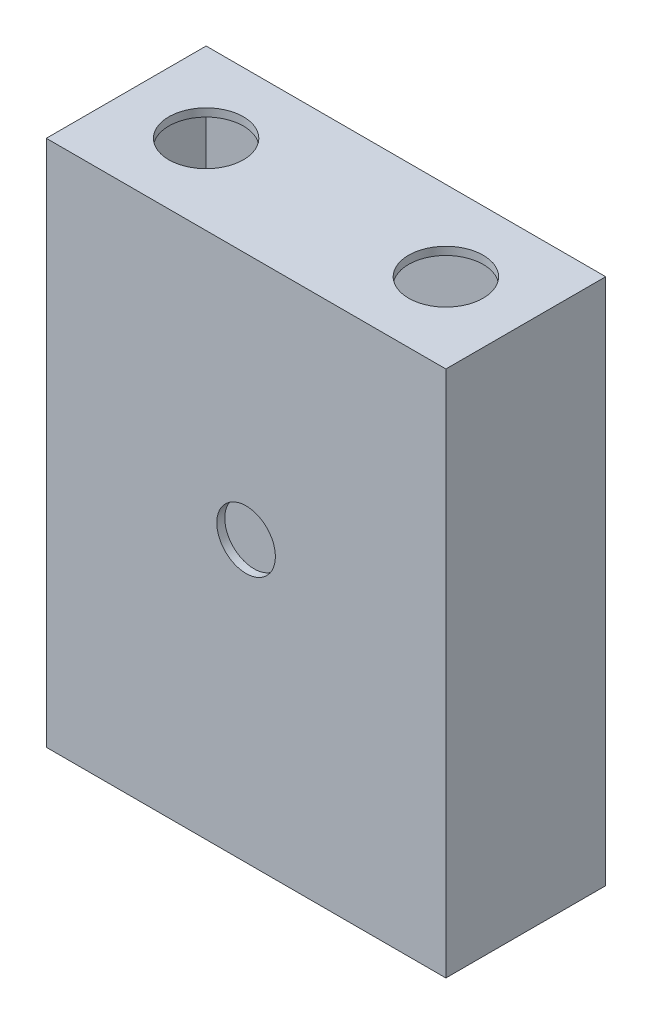
SolidWorks part; units mm, degrees
ref_plane "Alzado" through (0, 0, 0) normal (0, 0, 1) x (1, 0, 0)
ref_plane "Planta" through (0, 0, 0) normal (0, 1, 0) x (1, 0, 0)
ref_plane "Vista lateral" through (0, 0, 0) normal (1, 0, 0) x (0, 0, -1)
sketch "Croquis1" plane through (0, 0, 0) normal (0, 1, 0) x (1, 0, 0)
  line L1 (-120, -30) -> (120, -30)
  line L2 (-120, -30) -> (-120, 30)
  line L3 (-120, 30) -> (120, 30)
  line L4 (120, -30) -> (120, 30)
  line L5 (-120, -30) -> (120, 30) construction
  line L6 (-120, 30) -> (120, -30) construction
  circle A0 centre (0, 0) radius 14
  circle A1 centre (-90, 0) radius 14
  point P0 (0, 0)
  dimension "D3" = 28
  dimension "D4" = 28
  dimension "D5" = 30
  dimension "D6" = 90
  dimension "D1" = 240
  dimension "D2" = 60
extrude "Saliente-Extruir1" add sketch "Croquis1" along normal blind 3
sketch "Croquis4" plane through (0, 3, 0) normal (0, 1, 0) x (1, 0, 0)
  line L0 (-120, -30) -> (120, -30) construction
  line L1 (120, 30) -> (30, 30)
  line L2 (120, 30) -> (120, -30)
  line L3 (120, -30) -> (30, -30)
  line L4 (30, 30) -> (30, -30)
  dimension "D1" = 90
  dimension "D2" = 30
extrude "Cortar-Extruir2" cut sketch "Croquis4" against normal blind 5
sketch "Croquis2" plane through (0, 0, 0) normal (0, -1, 0) x (1, 0, 0)
  line L8 (-117, -27) -> (-117, 27)
  line L9 (-120, -30) -> (30, -30)
  line L10 (-120, -30) -> (-120, 30)
  line L11 (-120, 30) -> (30, 30)
  line L12 (30, -30) -> (30, 30)
  line L13 (-117, 27) -> (27, 27)
  line L14 (27, -27) -> (27, 27)
  line L15 (-117, -27) -> (27, -27)
  dimension "D1" = 3
extrude "Saliente-Extruir2" add sketch "Croquis2" along normal blind 195
sketch "Croquis5" plane through (0, 0, 30) normal (0, 0, 1) x (1, 0, 0)
  line L0 (-45, -195) -> (-45, -90) construction
  line L1 (30, -195) -> (-120, -195) construction
  circle A0 centre (-45, -90) radius 11
  dimension "D1" = 22
  dimension "D2" = 105
extrude "Cortar-Extruir3" cut sketch "Croquis5" against normal blind 5
